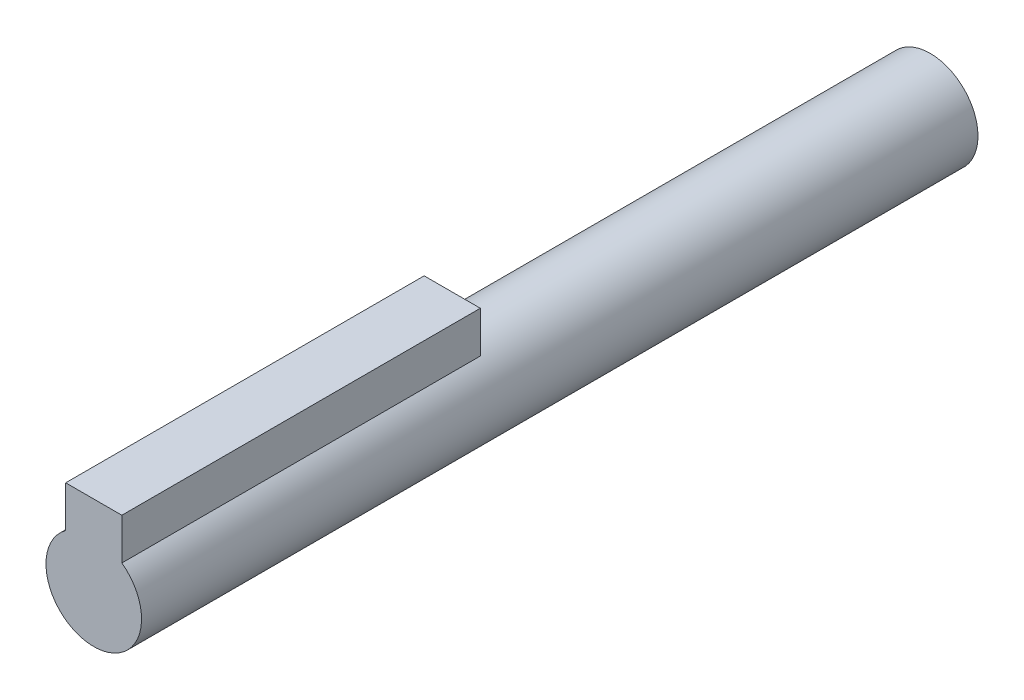
SolidWorks part; units mm, degrees
ref_plane "Front Plane" through (0, 0, 0) normal (0, 0, 1) x (1, 0, 0)
ref_plane "Top Plane" through (0, 0, 0) normal (0, 1, 0) x (1, 0, 0)
ref_plane "Right Plane" through (0, 0, 0) normal (1, 0, 0) x (0, 0, -1)
sketch "Sketch1" plane through (0, 0, 0) normal (0, 0, 1) x (1, 0, 0)
  circle A0 centre (0, 0) radius 4
  dimension "D1" = 8
extrude "Boss-Extrude1" add sketch "Sketch1" along normal blind 70
sketch "Sketch2" plane through (0, 0, 70) normal (0, 0, 1) x (1, 0, 0)
  line L0 (0, 0) -> (0, 8.6) construction
  line L2 (-2.35, 1.3) -> (2.35, 1.3)
  line L3 (-2.35, 1.3) -> (-2.35, 6.7)
  line L4 (-2.35, 6.7) -> (2.35, 6.7)
  line L5 (2.35, 1.3) -> (2.35, 6.7)
  line L6 (-2.35, 1.3) -> (2.35, 6.7) construction
  line L7 (-2.35, 6.7) -> (2.35, 1.3) construction
  circle A0 centre (0, 0) radius 4 construction
  point P3 (0, 4)
  dimension "D1" = 6.7
  dimension "D2" = 4.7
extrude "Boss-Extrude4" add sketch "Sketch2" against normal blind 30
